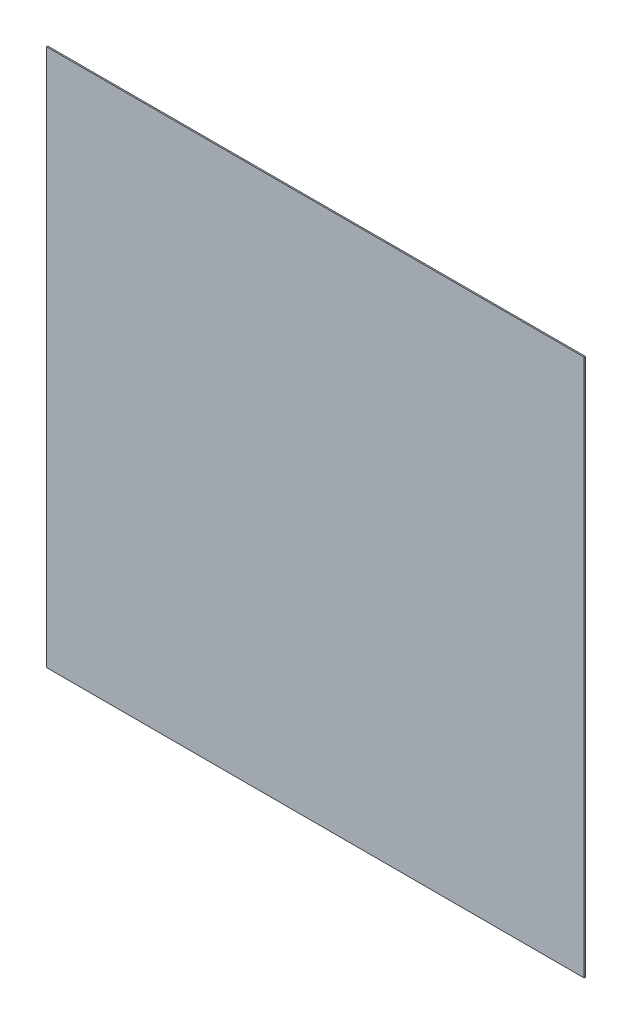
SolidWorks part; units mm, degrees
ref_plane "Front" through (0, 0, 0) normal (0, 0, 1) x (1, 0, 0)
ref_plane "Top" through (0, 0, 0) normal (0, 1, 0) x (1, 0, 0)
ref_plane "Right" through (0, 0, 0) normal (1, 0, 0) x (0, 0, -1)
sketch "Sketch1" plane through (0, 0, 0) normal (0, 0, 1) x (1, 0, 0)
  line L1 (-313, 313) -> (313, 313)
  line L2 (-313, 313) -> (-313, -313)
  line L3 (-313, -313) -> (313, -313)
  line L4 (313, 313) -> (313, -313)
  line L5 (-313, 313) -> (313, -313) construction
  line L6 (-313, -313) -> (313, 313) construction
  point P0 (0, 0)
  dimension "D1" = 626
  dimension "D2" = 626
extrude "Boss-Extrude1" add sketch "Sketch1" along normal blind 1.5
sketch "Sketch2" plane through (0, 0, 0) normal (0, 0, -1) x (-1, 0, 0)
  line L0 (-313, 313) -> (313, 313) construction
  line L2 (-91.4177, 0) -> (78.2357, 0) construction
  line L3 (0, 61.169) -> (0, -78.8952) construction
  line L4 (-313, -313) -> (-313, 313) construction
  circle A0 centre (0, 293) radius 5
  circle A1 centre (-293, 0) radius 5
  circle A2 centre (0, -293) radius 5
  circle A3 centre (293, 0) radius 5
  point P5 (0, 0)
  dimension "D1" = 10
  dimension "D4" = 10
  dimension "D2" = 20
  dimension "D3" = 0
  dimension "D5" = 20
  dimension "D6" = 0
extrude "Boss-Extrude2" add sketch "Sketch2" along normal blind 1.5
